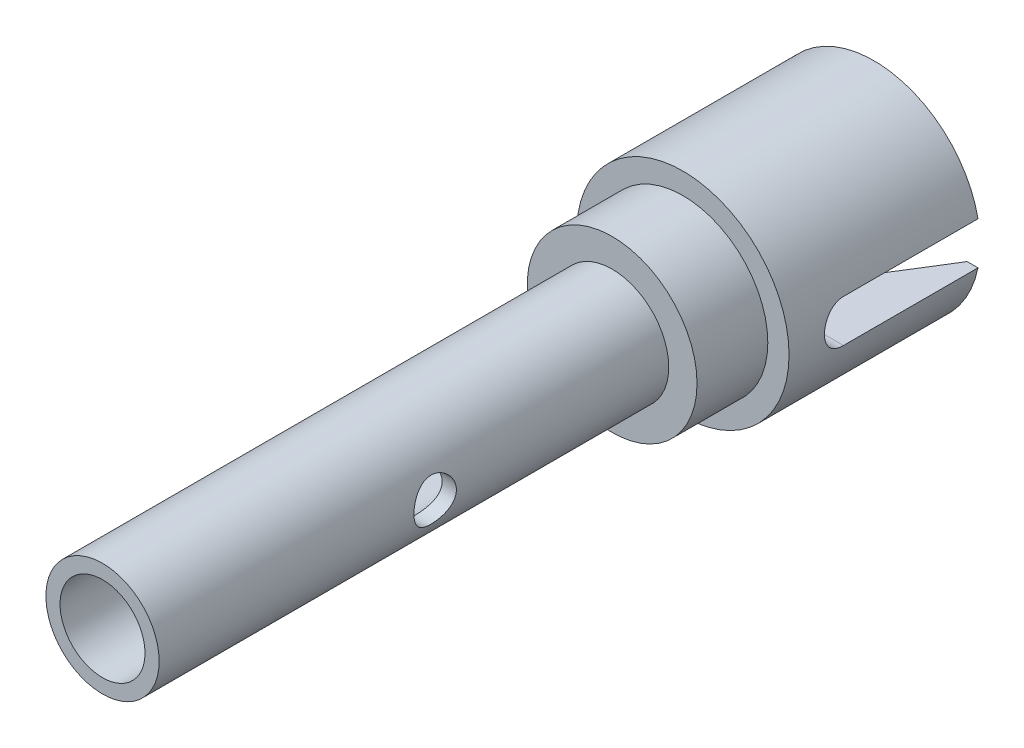
SolidWorks part; units mm, degrees
material "AISI 1020"
ref_plane "Front Plane" through (0, 0, 0) normal (0, 0, 1) x (1, 0, 0)
ref_plane "Top Plane" through (0, 0, 0) normal (0, 1, 0) x (1, 0, 0)
ref_plane "Right Plane" through (0, 0, 0) normal (1, 0, 0) x (0, 0, -1)
sketch "Sketch1" plane through (0, 0, 0) normal (1, 0, 0) x (0, 0, -1)
  line L0 (0, 0) -> (54.5, 0) construction
  line L1 (0, 4) -> (36, 4)
  line L2 (36, 4) -> (36, 6)
  line L3 (36, 6) -> (41, 6)
  line L4 (41, 6) -> (41, 7.5)
  line L5 (41, 7.5) -> (54.5, 7.5)
  line L6 (54.5, 7.5) -> (54.5, 0)
  line L7 (0, 4) -> (0, 0)
  line L8 (0, 0) -> (54.5, 0)
  dimension "D1" = 54.5
  dimension "D2" = 4
  dimension "D3" = 6
  dimension "D4" = 7.5
  dimension "D5" = 18.5
  dimension "D6" = 13.5
  dimension "D7" = 0
revolve "Revolve1" add sketch "Sketch1" angle 360 about L0
sketch "Sketch2" plane through (0, 0, 0) normal (1, 0, 0) x (0, 0, -1)
  line L0 (54.5, 0) -> (36, 0) construction
  line L1 (54.5, -7.5) -> (54.5, 7.5) construction
  line L2 (36, 4) -> (36, -4) construction
  line L3 (54.5, 0) -> (45, 0) construction
  line L4 (54.5, -1.5) -> (45, -1.5)
  line L5 (54.5, 1.5) -> (45, 1.5)
  arc A0 (54.5, -1.5) -> (54.5, 1.5) centre (54.5, 0) ccw
  arc A1 (45, 1.5) -> (45, -1.5) centre (45, 0) ccw
  point P6 (49.75, 0)
  dimension "D2" = 9.5
  dimension "D1" = 3
extrude "Cut-Extrude1" cut sketch "Sketch2" against normal through all both and the other way through all
sketch "Sketch3" plane through (0, 0, -54.5) normal (0, 0, -1) x (-1, 0, 0)
  circle A0 centre (0, 0) radius 3.75
  dimension "D1" = 7.5
extrude "Cut-Extrude2" cut sketch "Sketch3" against normal offset from surface (11.5 mm away) 2 up to face at (6, 0, -41)
chamfer "Chamfer1" distance 3 distance2 5 2 edges at (0, -3.75, -54.5) (0, 3.75, -54.5)
sketch "Sketch4" plane through (0, 0, 0) normal (0, 0, 1) x (1, 0, 0)
  circle A0 centre (0, 0) radius 3
  dimension "D1" = 6
extrude "Cut-Extrude3" cut sketch "Sketch4" against normal blind 27.5
sketch "Sketch5" plane through (0, 0, 0) normal (1, 0, 0) x (0, -1, 0)
  line L0 (0, 0) -> (0, 43.5) construction
  line L2 (-4, 0) -> (4, 0) construction
  circle A0 centre (0, 19.5) radius 1.5
  arc A1 (-1.5, 45) -> (1.5, 45) centre (0, 45) ccw construction
  dimension "D1" = 3
  dimension "D2" = 19.5
extrude "Cut-Extrude4" cut sketch "Sketch5" against normal through all both and the other way through all
ref_plane "Plane1" through (0, 0, 0) normal (0, 1, 0) x (1, 0, 0)
